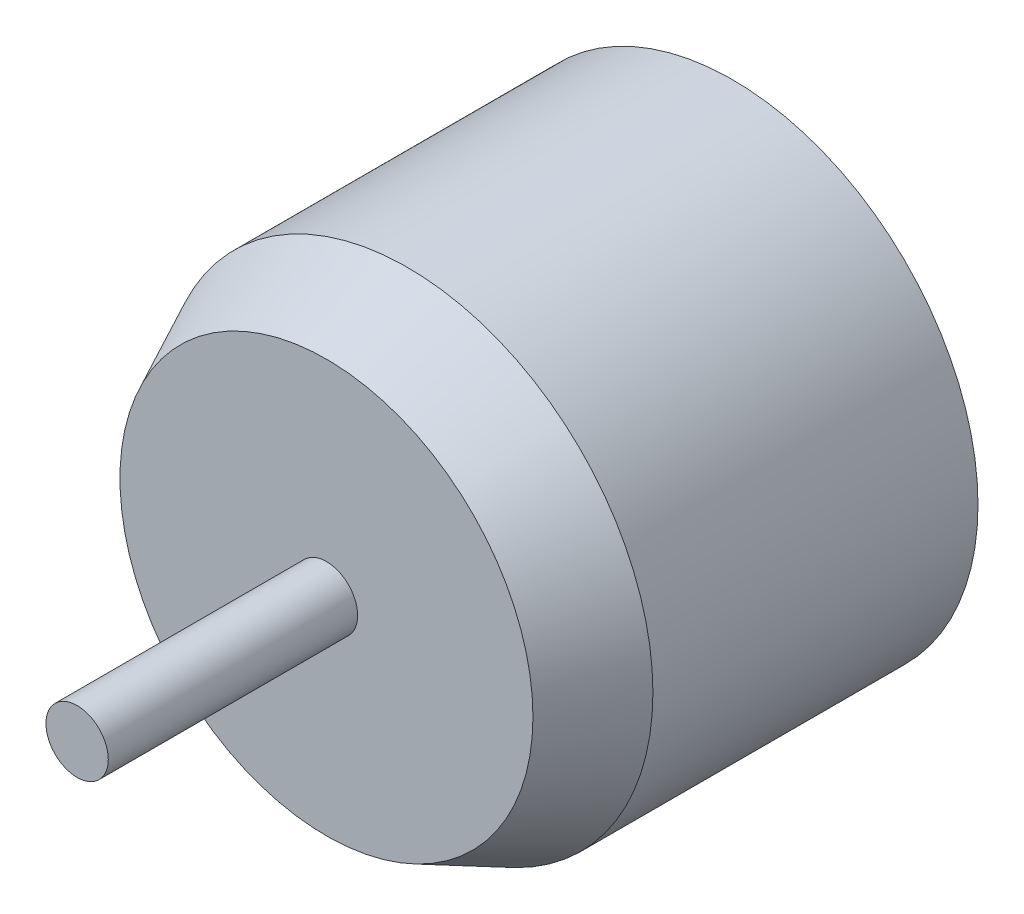
SolidWorks part; units mm, degrees
ref_plane "Front Plane" through (0, 0, 0) normal (0, 0, 1) x (1, 0, 0)
ref_plane "Top Plane" through (0, 0, 0) normal (0, 1, 0) x (1, 0, 0)
ref_plane "Right Plane" through (0, 0, 0) normal (1, 0, 0) x (0, 0, -1)
sketch "Sketch1" plane through (0, 0, 0) normal (1, 0, 0) x (0, 0, -1)
  line L0 (-164.6094, 0) -> (171.7188, 0) construction
  line L1 (-102.7529, 0) -> (-15.7529, 0)
  line L2 (-15.7529, 0) -> (-15.7529, 22.2916)
  line L3 (-15.7529, 22.2916) -> (-18.6398, 31.5)
  line L4 (-18.6398, 31.5) -> (-60.3587, 31.5)
  line L5 (-60.3587, 31.5) -> (-70.7529, 26.4985)
  line L6 (-70.7529, 26.4985) -> (-70.7529, 4)
  line L7 (-70.7529, 4) -> (-102.7529, 4)
  line L8 (-102.7529, 4) -> (-102.7529, 0)
  point P5 (-24.9791, 120.9118)
  point P12 (-18.1797, 24.7137)
  point P13 (-70.7529, 26.4985)
  point P14 (0, 0)
  point P15 (-18.6398, 31.5)
  point P16 (0, 0)
  dimension "D1" = 32
  dimension "D2" = 55
  dimension "D3" = 31.5
  dimension "D4" = 4
revolve "Revolve1" add sketch "Sketch1" angle 360 about L0
